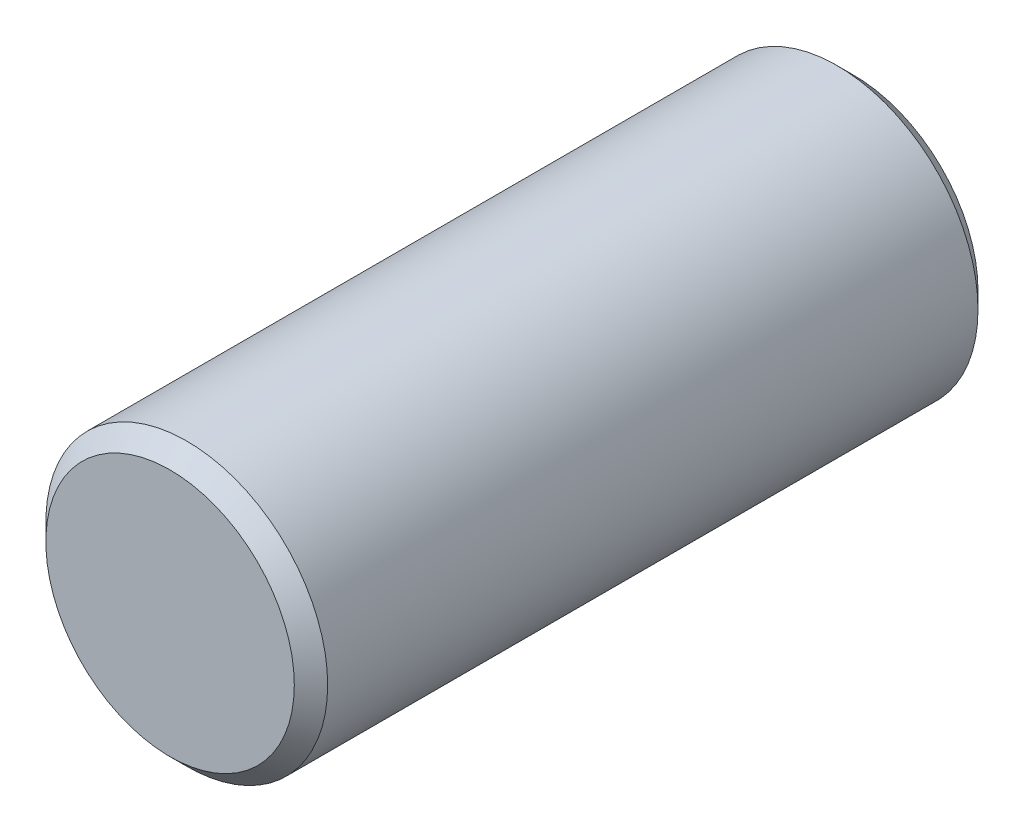
SolidWorks part; units mm, degrees
ref_plane "Front Plane" through (0, 0, 0) normal (0, 0, 1) x (1, 0, 0)
ref_plane "Top Plane" through (0, 0, 0) normal (0, 1, 0) x (1, 0, 0)
ref_plane "Right Plane" through (0, 0, 0) normal (1, 0, 0) x (0, 0, -1)
sketch "Sketch1" plane through (0, 0, 0) normal (0, 0, 1) x (1, 0, 0)
  circle A0 centre (0, 0) radius 429.26
  dimension "D1" = 858.52
extrude "Boss-Extrude1" add sketch "Sketch1" along normal mid plane 2082.8
chamfer "Chamfer1" distance 50.8 angle 45 2 edges at (429.26, 0, 1041.4) (429.26, 0, -1041.4)
